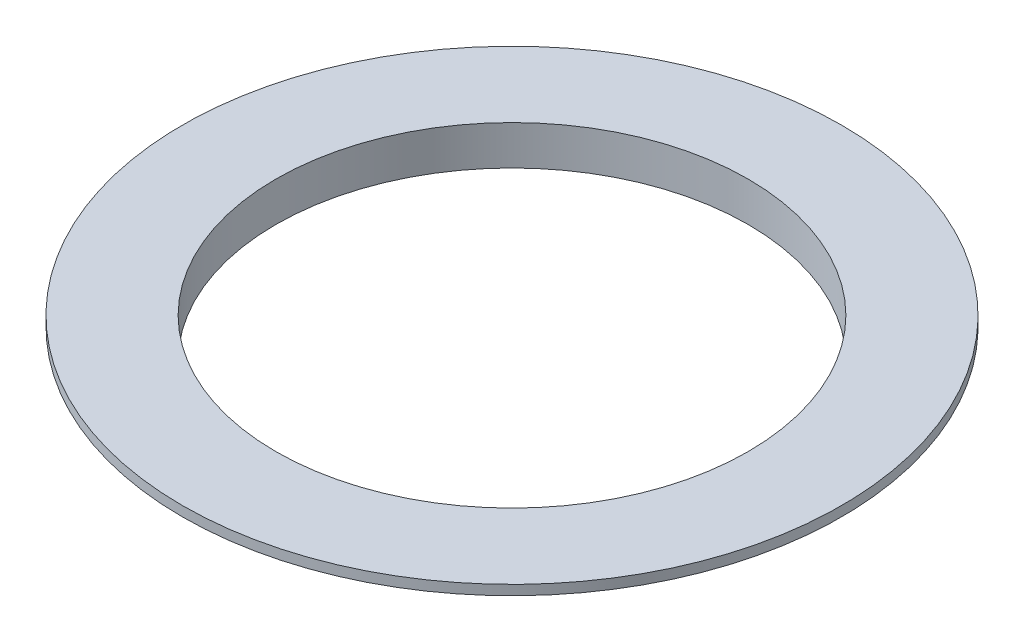
SolidWorks part; units mm, degrees
material "PVC Rigid"
ref_plane "Front Plane" through (0, 0, 0) normal (0, 0, 1) x (1, 0, 0)
ref_plane "Top Plane" through (0, 0, 0) normal (0, 1, 0) x (1, 0, 0)
ref_plane "Right Plane" through (0, 0, 0) normal (1, 0, 0) x (0, 0, -1)
sketch "Sketch1" plane through (0, 0, 0) normal (1, 0, 0) x (0, 0, -1)
  line L0 (50.8, 0) -> (80.9625, 0)
  line L1 (80.9625, 0) -> (80.9625, 9.525)
  line L2 (80.9625, 9.525) -> (106.3625, 9.525)
  line L3 (106.3625, 9.525) -> (106.3625, 12.7)
  line L4 (106.3625, 12.7) -> (0, 12.7)
  line L5 (0, 12.7) -> (0, 9.525)
  line L6 (0, 9.525) -> (50.8, 9.525)
  line L7 (50.8, 9.525) -> (50.8, 0)
  line L8 (0, 0) -> (0, 12.7) construction
  dimension "D1" = 12.7
  dimension "D2" = 3.175
  dimension "D3" = 80.9625
  dimension "D4" = 106.3625
  dimension "D5" = 50.8
  dimension "D6" = 12.7
revolve "Revolve1" add sketch "Sketch1" angle 360 about L8
sketch "Sketch4" plane through (0, 12.7, 0) normal (0, 1, 0) x (1, 0, 0)
  circle A0 centre (0, 0) radius 76.2
  dimension "D1" = 152.4
extrude "Cut-Extrude1" cut sketch "Sketch4" against normal through all
